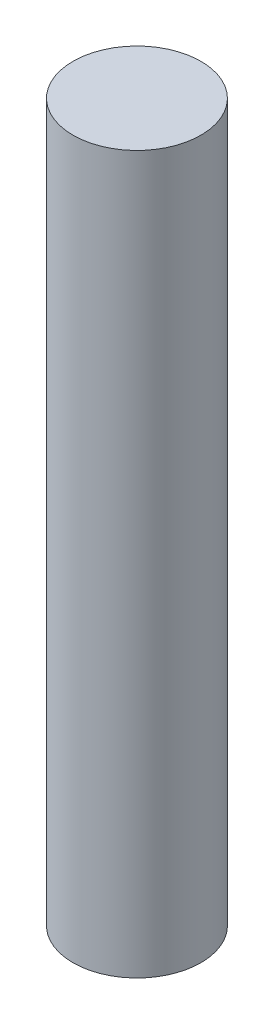
SolidWorks part; units mm, degrees
ref_plane "Front Plane" through (0, 0, 0) normal (0, 0, 1) x (1, 0, 0)
ref_plane "Top Plane" through (0, 0, 0) normal (0, 1, 0) x (1, 0, 0)
ref_plane "Right Plane" through (0, 0, 0) normal (1, 0, 0) x (0, 0, -1)
sketch "Sketch1" plane through (0, 0, 0) normal (0, 1, 0) x (1, 0, 0)
  circle A0 centre (0, 0) radius 12.5
  dimension "D1" = 25
extrude "Boss-Extrude1" add sketch "Sketch1" along normal blind 140
